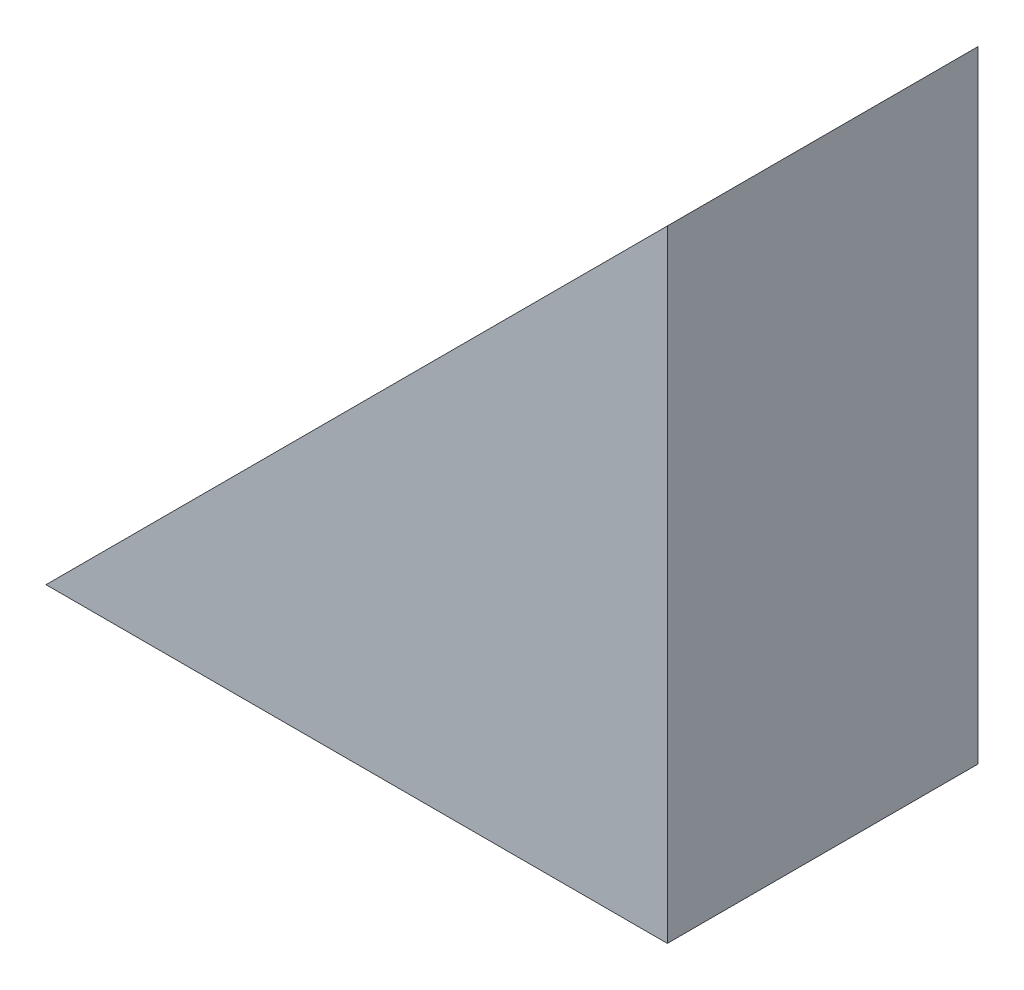
SolidWorks part; units mm, degrees
ref_plane "Front Plane" through (0, 0, 0) normal (0, 0, 1) x (1, 0, 0)
ref_plane "Top Plane" through (0, 0, 0) normal (0, 1, 0) x (1, 0, 0)
ref_plane "Right Plane" through (0, 0, 0) normal (1, 0, 0) x (0, 0, -1)
sketch "Sketch1" plane through (0, 0, 0) normal (0, 0, 1) x (1, 0, 0)
  line L0 (0, 0) -> (0, 20)
  line L1 (0, 20) -> (-20, 0)
  line L2 (-20, 0) -> (0, 0)
  dimension "D1" = 20
extrude "Boss-Extrude1" add sketch "Sketch1" along normal blind 10
